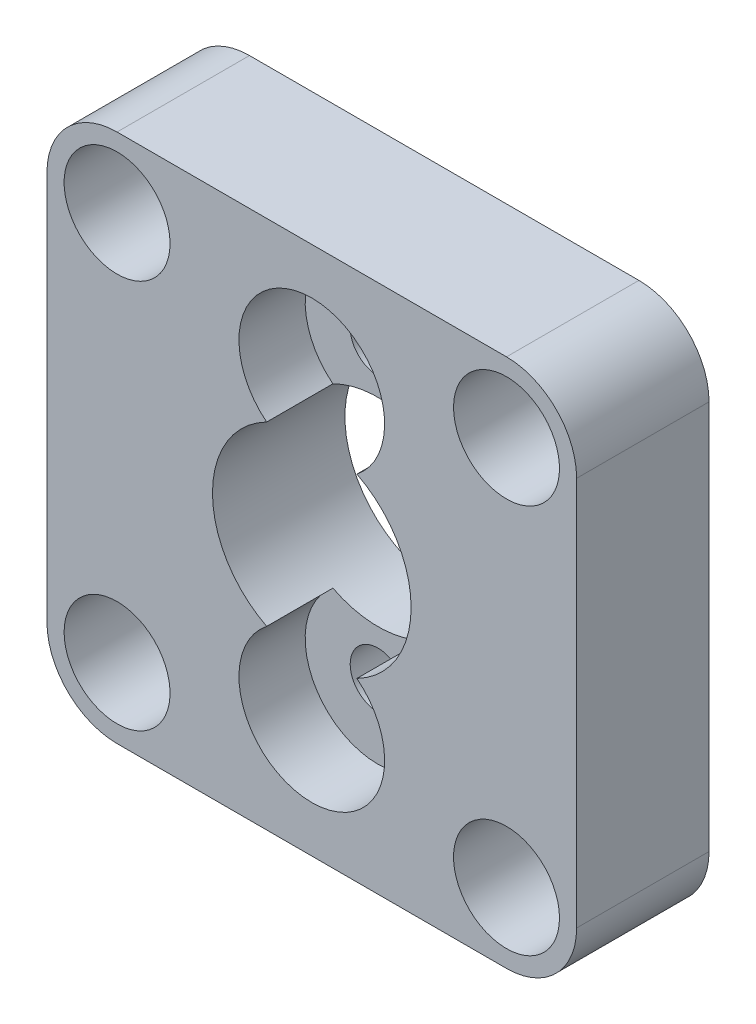
SolidWorks part; units mm, degrees
ref_plane "Ebene vorne" through (0, 0, 0) normal (0, 0, 1) x (1, 0, 0)
ref_plane "Ebene oben" through (0, 0, 0) normal (0, 1, 0) x (1, 0, 0)
ref_plane "Ebene rechts" through (0, 0, 0) normal (1, 0, 0) x (0, 0, -1)
sketch "Skizze2" plane through (0, 0, 0) normal (1, 0, 0) x (0, 0, -1)
  line L0 (0, 3.75) -> (-1, 3.75)
  line L1 (-1, 3.75) -> (-1, 3.25)
  line L2 (-1, 3.25) -> (-2.6, 3.25)
  line L3 (-2.6, 3.25) -> (-2.6, 2)
  line L4 (-2.6, 2) -> (-5, 2)
  line L5 (-5, 2) -> (-5, 7.5)
  line L6 (-5, 7.5) -> (0, 7.5)
  line L7 (0, 7.5) -> (0, 3.75)
  line L8 (0, 7.5) -> (0, -7.5) construction
  line L9 (0, 3.5) -> (-1, 3.5) construction
  line L10 (-1, 3) -> (-2.6, 3) construction
  line L11 (-2.6, 1.5) -> (-12.3, 1.5) construction
  line L12 (-1, 3.5) -> (-1, -3.5) construction
  line L13 (-2.6, 3) -> (-2.6, -3) construction
  line L14 (11.7, 7.5) -> (0, 7.5) construction
  line L15 (-12.6, 0) -> (-4.4763, 0) construction
  line L16 (-12.6, 1.3601) -> (-12.6, -1.3601) construction
  dimension "D1" = 0.25
  dimension "D2" = 0.25
  dimension "D3" = 0.5
  dimension "D4" = 5
revolve "Rotation1" add sketch "Skizze2" angle 360 about L15
sketch "Skizze3" plane through (0, 0, 5) normal (0, 0, 1) x (1, 0, 0)
  line L1 (10, -10) -> (-10, -10)
  line L2 (10, -10) -> (10, 10)
  line L3 (10, 10) -> (-10, 10)
  line L4 (-10, -10) -> (-10, 10)
  line L5 (10, -10) -> (-10, 10) construction
  line L6 (10, 10) -> (-10, -10) construction
  circle A0 centre (0, 0) radius 10 construction
  circle A1 centre (0, 0) radius 7.5
  circle A2 centre (0, 0) radius 7.5 construction
  point P0 (0, 0)
extrude "Aufsatz-Linear austragen2" add sketch "Skizze3" against normal through all
sketch "Skizze4" plane through (0, 0, 5) normal (0, 0, 1) x (1, 0, 0)
  line L0 (0, 0) -> (14.1772, 0) construction
  circle A0 centre (0, 5.5) radius 1.05
  circle A1 centre (0, 5.5) radius 0.8 construction
  circle A2 centre (0, -5.5) radius 1.05
  dimension "D1" = 0.25
extrude "Schnitt-Linear austragen1" cut sketch "Skizze4" against normal through all
sketch "Skizze5" plane through (0, 0, 5) normal (0, 0, 1) x (1, 0, 0)
  line L0 (0, 0) -> (11.8845, 0) construction
  circle A0 centre (0, 5.5) radius 2.75
  circle A1 centre (0, -5.5) radius 2.75
  dimension "D1" = 5.5
extrude "Schnitt-Linear austragen2" cut sketch "Skizze5" against normal blind 2.5
sketch "Skizze6" plane through (0, 0, 5) normal (0, 0, 1) x (1, 0, 0)
  line L0 (-10, 7.3523) -> (-10.8878, 7.3523)
  line L1 (-10.8878, 7.3523) -> (-10.8878, 10.8878)
  line L2 (-10.8878, 10.8878) -> (-7.3523, 10.8878)
  line L3 (-7.3523, 10.8878) -> (-7.3523, 10)
  line L4 (-10.8878, 10.8878) -> (-7.3523, 7.3523) construction
  line L5 (10, 10) -> (-10, 10) construction
  line L6 (-10, 10) -> (-10, -10) construction
  line L7 (0, 0) -> (0, 11.857) construction
  line L8 (0, 0) -> (17.2944, 0) construction
  line L9 (10.8878, 10.8878) -> (7.3523, 7.3523) construction
  line L10 (7.3523, 10.8878) -> (7.3523, 10)
  line L11 (10.8878, 10.8878) -> (7.3523, 10.8878)
  line L12 (10.8878, 7.3523) -> (10.8878, 10.8878)
  line L13 (10, 7.3523) -> (10.8878, 7.3523)
  line L14 (10.8878, -10.8878) -> (7.3523, -7.3523) construction
  line L15 (-10.8878, -10.8878) -> (-7.3523, -7.3523) construction
  line L16 (10, -7.3523) -> (10.8878, -7.3523)
  line L17 (10.8878, -7.3523) -> (10.8878, -10.8878)
  line L18 (10.8878, -10.8878) -> (7.3523, -10.8878)
  line L19 (7.3523, -10.8878) -> (7.3523, -10)
  line L20 (-7.3523, -10.8878) -> (-7.3523, -10)
  line L21 (-10.8878, -10.8878) -> (-7.3523, -10.8878)
  line L22 (-10.8878, -7.3523) -> (-10.8878, -10.8878)
  line L23 (-10, -7.3523) -> (-10.8878, -7.3523)
  arc A4 (-10, 7.3523) -> (-7.3523, 10) centre (-7.3523, 7.3523) cw
  arc A5 (-7.3523, 10) -> (-10, 7.3523) centre (-7.3523, 7.3523) ccw construction
  arc A6 (10, 7.3523) -> (7.3523, 10) centre (7.3523, 7.3523) ccw
  arc A7 (10, -7.3523) -> (7.3523, -10) centre (7.3523, -7.3523) cw
  arc A8 (-10, -7.3523) -> (-7.3523, -10) centre (-7.3523, -7.3523) ccw
  dimension "D1" = 5
extrude "Schnitt-Linear austragen3" cut sketch "Skizze6" against normal through all
sketch "Skizze7" plane through (0, 0, 5) normal (0, 0, 1) x (1, 0, 0)
  line L0 (0, 10) -> (0, 0) construction
  line L1 (7.3523, 10) -> (-7.3523, 10) construction
  line L2 (0, 0) -> (10, 0) construction
  line L3 (10, -7.3523) -> (10, 7.3523) construction
  circle A0 centre (-7.3523, 7.3523) radius 1.15
  circle A1 centre (7.3523, 7.3523) radius 1.15
  circle A2 centre (7.3523, -7.3523) radius 1.15
  circle A3 centre (-7.3523, -7.3523) radius 1.15
  circle A4 centre (-7.3523, 7.3523) radius 1.7 construction
  dimension "D1" = 2.3
extrude "Schnitt-Linear austragen4" cut sketch "Skizze7" against normal through all
sketch "Skizze8" plane through (0, 0, 5) normal (0, 0, 1) x (1, 0, 0)
  line L0 (0, 10) -> (0, 0) construction
  line L1 (7.3523, 10) -> (-7.3523, 10) construction
  line L2 (0, 0) -> (10, 0) construction
  line L3 (10, -7.3523) -> (10, 7.3523) construction
  circle A0 centre (-7.3523, 7.3523) radius 2
  circle A1 centre (7.3523, 7.3523) radius 2
  circle A2 centre (7.3523, -7.3523) radius 2
  circle A3 centre (-7.3523, -7.3523) radius 2
  dimension "D1" = 4
extrude "Schnitt-Linear austragen5" cut sketch "Skizze8" against normal blind 3
sketch "Skizze10" plane through (0, 0, 0) normal (0, 0, -1) x (-1, 0, 0)
  circle A0 centre (0, 0) radius 3.75
  circle A1 centre (0, 0) radius 3.75 construction
extrude "Schnitt-Linear austragen6" cut sketch "Skizze10" against normal through all
equation "\"M2EinschmelzGewindeDurchmesser\"= 3.4"
equation "\"M2EinschmelzGewindeTiefe\"= 4"
equation "\"M3EinschmelzGewindeDurchmesser\"= 4.2"
equation "\"M3EinschmelzGewindeTief\"= 5.7"
equation "\"M2SchraubeLoch\"=2.3"
equation "\"D1@Skizze7\"=\"M2SchraubeLoch\""
